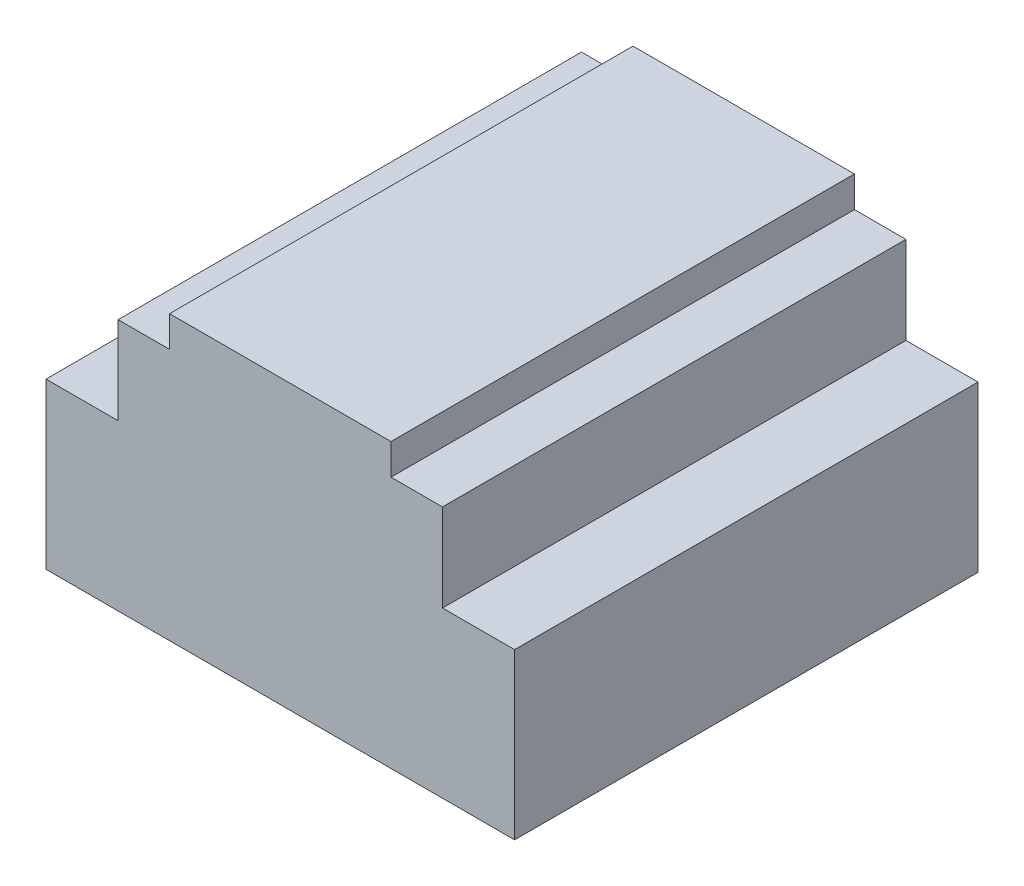
SolidWorks part; units mm, degrees
ref_plane "Front Plane" through (0, 0, 0) normal (0, 0, 1) x (1, 0, 0)
ref_plane "Top Plane" through (0, 0, 0) normal (0, 1, 0) x (1, 0, 0)
ref_plane "Right Plane" through (0, 0, 0) normal (1, 0, 0) x (0, 0, -1)
sketch "Sketch1" plane through (0, 0, 0) normal (0, 0, 1) x (1, 0, 0)
  line L1 (0, 0) -> (91, 0)
  line L2 (0, 0) -> (0, 55)
  line L3 (0, 55) -> (91, 55)
  line L4 (91, 0) -> (91, 55)
  dimension "D1" = 91
  dimension "D2" = 55
extrude "Boss-Extrude1" add sketch "Sketch1" along normal blind 90
sketch "Sketch2" plane through (0, 0, 90) normal (0, 0, 1) x (1, 0, 0)
  line L0 (45.5, 55) -> (45.5, 33.7592) construction
  line L1 (91, 55) -> (0, 55) construction
  line L2 (91, 0) -> (91, 55) construction
  line L3 (24, 55) -> (67, 55)
  line L4 (67, 49) -> (67, 55)
  line L5 (24, 55) -> (0, 55)
  line L6 (0, 55) -> (1.5083, 56.5083)
  line L7 (67, 55) -> (91, 55)
  line L8 (67, 49) -> (67, 55)
  line L9 (67, 49) -> (91, 49)
  line L10 (91, 55) -> (91, 49)
  line L11 (24, 55) -> (24, 49)
  line L12 (24, 55) -> (0, 55)
  line L13 (0, 55) -> (0, 49)
  line L14 (24, 49) -> (0, 49)
  line M8 (0, 55) -> (0, 0)
  line M10 (91, 0) -> (91, 55)
  line M11 (91, 55) -> (0, 55)
  dimension "D1" = 43
  dimension "D3" = 6
extrude "Cut-Extrude1" cut sketch "Sketch2" against normal through all contours L4 L9 M10 M11 | L14 L11 M11 M8
sketch "Sketch3" plane through (0, 0, 90) normal (0, 0, 1) x (1, 0, 0)
  line L0 (0, 0) -> (91, 0) construction
  line L1 (91, 49) -> (77, 49)
  line L2 (91, 49) -> (91, 32)
  line L3 (91, 32) -> (77, 32)
  line L4 (77, 49) -> (77, 32)
  line L5 (45.5, 55) -> (45.5, 40.7913) construction
  line L6 (67, 55) -> (24, 55) construction
  line L7 (0, 32) -> (14, 32)
  line L8 (0, 49) -> (0, 32)
  line L9 (0, 49) -> (14, 49)
  line L10 (14, 49) -> (14, 32)
  dimension "D1" = 14
  dimension "D2" = 49
  dimension "D3" = 32
extrude "Cut-Extrude2" cut sketch "Sketch3" against normal through all
